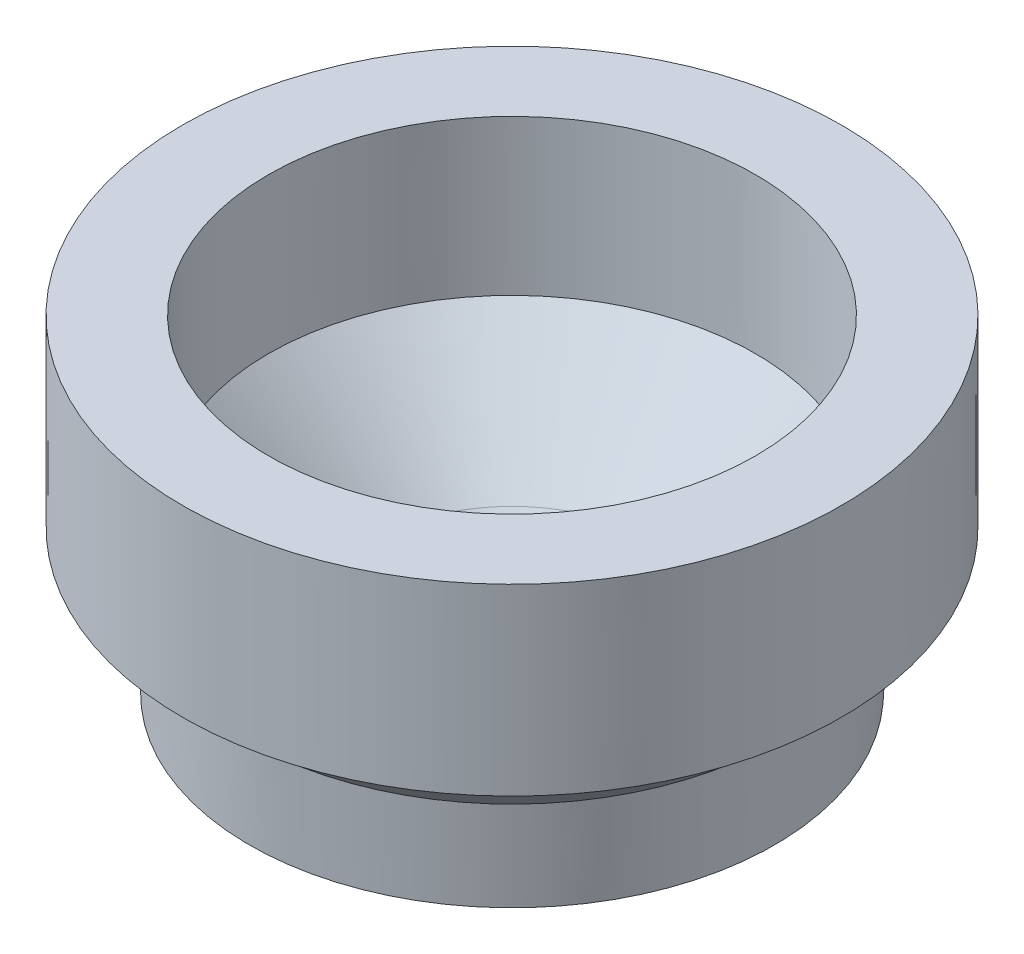
SolidWorks part; units mm, degrees
material "1.4003 (X2CrNi12)"
ref_plane "Front Plane" through (0, 0, 0) normal (0, 0, 1) x (1, 0, 0)
ref_plane "Top Plane" through (0, 0, 0) normal (0, 1, 0) x (1, 0, 0)
ref_plane "Right Plane" through (0, 0, 0) normal (1, 0, 0) x (0, 0, -1)
sketch "Sketch1" plane through (0, 0, 0) normal (0, 0, 1) x (1, 0, 0)
  line L0 (0.0002, 3.4611) -> (0, 0)
  line L1 (10.2184, 0) -> (12.1903, 1.3904)
  line L2 (12.1903, 1.3904) -> (12.3906, 5.6974)
  line L3 (12.3906, 5.6974) -> (15.0256, 8.0735)
  line L4 (15.0256, 8.0735) -> (15.2941, 8.0736)
  line L5 (15.2941, 8.0736) -> (15.2941, 16.5885)
  line L6 (15.2941, 16.5885) -> (11.3065, 16.5885)
  line L7 (11.3065, 16.5885) -> (11.3065, 9.3923)
  line L8 (11.3065, 9.3923) -> (6.4662, 4.3363)
  line L9 (4.5278, 3.4611) -> (0.0002, 3.4611)
  line L10 (0, 0) -> (10.2184, 0)
  arc A0 (4.5278, 3.4611) -> (6.4662, 4.3363) centre (4.5315, 6.0372) ccw
revolve "Revolve1" add sketch "Sketch1" angle 360 about L0
